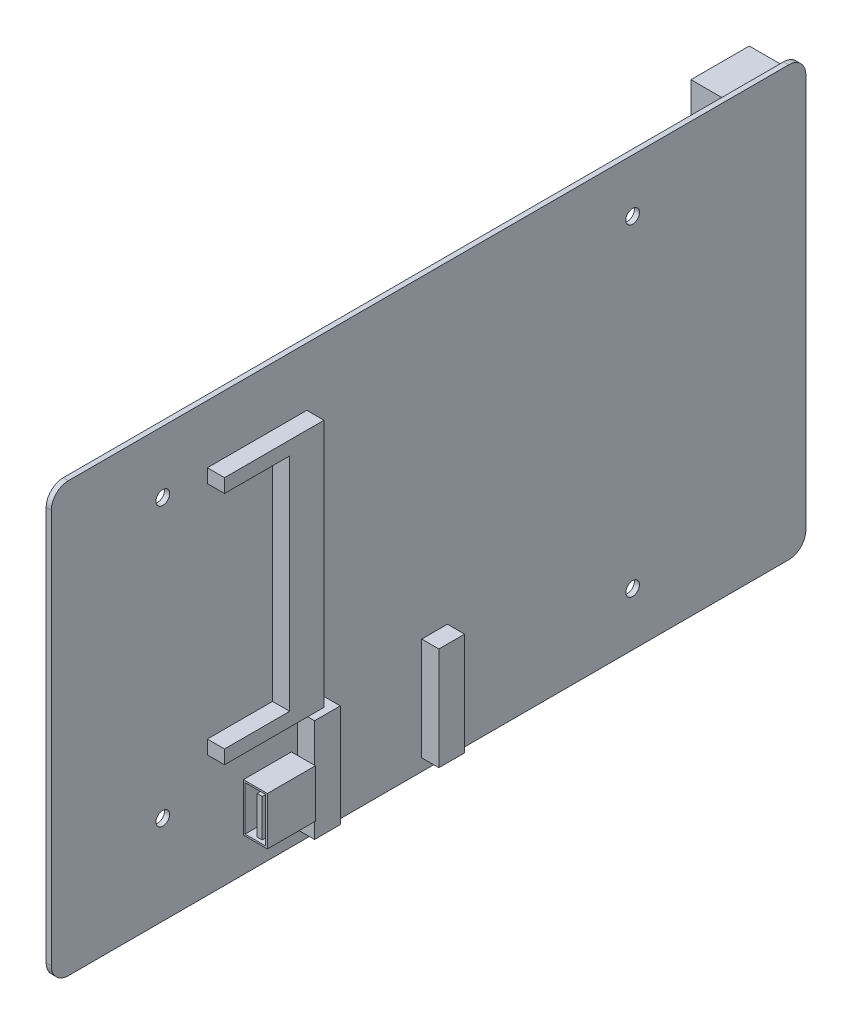
SolidWorks part; units mm, degrees
ref_plane "前视基准面" through (0, 0, 0) normal (0, 0, 1) x (1, 0, 0)
ref_plane "上视基准面" through (0, 0, 0) normal (0, 1, 0) x (1, 0, 0)
ref_plane "右视基准面" through (0, 0, 0) normal (1, 0, 0) x (0, 0, -1)
sketch "草图1" plane through (0, 0, 0) normal (1, 0, 0) x (0, 0, -1)
  line L1 (110, 62.5) -> (-110, 62.5)
  line L2 (110, 62.5) -> (110, -62.5)
  line L3 (110, -62.5) -> (-110, -62.5)
  line L4 (-110, 62.5) -> (-110, -62.5)
  line L5 (110, 62.5) -> (-110, -62.5) construction
  line L6 (110, -62.5) -> (-110, 62.5) construction
  point P0 (0, 0)
  dimension "D1" = 220
  dimension "D2" = 125
extrude "凸台-拉伸1" add sketch "草图1" against normal blind 1.5
fillet "圆角1" radius 5 4 edges at (-0.75, -62.5, -110) (-0.75, -62.5, 110) (-0.75, 62.5, -110) (-0.75, 62.5, 110)
sketch "草图2" plane through (0, 0, 0) normal (1, 0, 0) x (0, 0, -1)
  line L0 (-105, -62.5) -> (105, -62.5) construction
  line L1 (-39, -27.5) -> (-5, -27.5) construction
  line L2 (-39, -27.5) -> (-39, -60.5) construction
  line L3 (-39, -60.5) -> (-5, -60.5) construction
  line L4 (60, -27.5) -> (60, -60.5) construction
  line L5 (-39, -27.5) -> (60, -60.5) construction
  line L6 (-39, -60.5) -> (60, -27.5) construction
  line L7 (-73, 48.5) -> (-35.5, 48.5) construction
  line L8 (-73, 48.5) -> (-73, -30) construction
  line L9 (-73, -30) -> (-35.5, -30) construction
  line L10 (-35.5, 48.5) -> (-35.5, -30) construction
  line L11 (-73, 48.5) -> (-35.5, -30) construction
  line L12 (-73, -30) -> (-35.5, 48.5) construction
  line L13 (-110, 57.5) -> (-110, -57.5) construction
  line L14 (105, 62.5) -> (-105, 62.5) construction
  line L15 (-35.5, 45.5) -> (-64.5, 45.5)
  line L16 (-64.5, 45.5) -> (-64.5, 41.5)
  line L17 (-64.5, 41.5) -> (-45.5, 41.5)
  line L18 (-45.5, 41.5) -> (-45.5, -23)
  line L19 (-45.5, -23) -> (-64.5, -23)
  line L20 (-64.5, -23) -> (-64.5, -27)
  line L21 (-64.5, -27) -> (-35.5, -27)
  line L22 (-35.5, -27) -> (-35.5, 45.5)
  line L23 (-5, -27.5) -> (-5, -60.5) construction
  line L24 (-3.5, -27.5) -> (-3.5, -60.5) construction
  line L25 (-3.5, -27.5) -> (60, -27.5) construction
  line L26 (-3.5, -60.5) -> (60, -60.5) construction
  line L28 (-38.25, -29) -> (-30.75, -29)
  line L29 (-38.25, -29) -> (-38.25, -59)
  line L30 (-38.25, -59) -> (-30.75, -59)
  line L31 (-30.75, -29) -> (-30.75, -59)
  line L32 (-2, -29) -> (5.5, -29)
  line L33 (-2, -29) -> (-2, -59)
  line L34 (-2, -59) -> (5.5, -59)
  line L35 (5.5, -29) -> (5.5, -59)
  point P0 (10.5, -44)
  point P5 (-54.25, 9.25)
  dimension "D1" = 33
  dimension "D2" = 99
  dimension "D3" = 2
  dimension "D4" = 71
  dimension "D5" = 37.5
  dimension "D6" = 37
  dimension "D7" = 14
  dimension "D8" = 78.5
  dimension "D9" = 3
  dimension "D10" = 4
  dimension "D11" = 4
  dimension "D12" = 3
  dimension "D13" = 29
  dimension "D14" = 10
  dimension "D15" = 34
  dimension "D16" = 1.5
  dimension "D17" = 1.5
  dimension "D18" = 30
  dimension "D19" = 1.5
  dimension "D20" = 7.5
  dimension "D21" = 1.5
extrude "凸台-拉伸2" add sketch "草图2" along normal blind 5
sketch "草图3" plane through (0, 0, 0) normal (1, 0, 0) x (0, 0, -1)
  line L0 (-39, -27.5) -> (-39, -60.5) construction
  line L1 (-54, -38.5) -> (-40, -38.5)
  line L2 (-54, -38.5) -> (-54, -52.5)
  line L3 (-54, -52.5) -> (-40, -52.5)
  line L4 (-40, -38.5) -> (-40, -52.5)
  line L5 (-105, -62.5) -> (105, -62.5) construction
  dimension "D1" = 1
  dimension "D2" = 14
  dimension "D3" = 14
  dimension "D4" = 10
extrude "凸台-拉伸3" add sketch "草图3" along normal blind 7
sketch "草图4" plane through (0, 0, 54) normal (0, 0, 1) x (1, 0, 0)
  line L0 (7, -38.5) -> (0, -38.5) construction
  line L1 (0.5, -39) -> (6.5, -39)
  line L2 (0.5, -39) -> (0.5, -52)
  line L3 (0.5, -52) -> (6.5, -52)
  line L4 (6.5, -39) -> (6.5, -52)
  line L5 (4, -40) -> (5.5, -40)
  line L6 (4, -40) -> (4, -51)
  line L7 (4, -51) -> (5.5, -51)
  line L8 (5.5, -40) -> (5.5, -51)
  line L9 (7, -38.5) -> (7, -52.5) construction
  line L10 (7, -52.5) -> (0, -52.5) construction
  line L11 (0, -27.5) -> (0, -60.5) construction
  dimension "D1" = 0.5
  dimension "D2" = 0.5
  dimension "D3" = 0.5
  dimension "D4" = 0.5
  dimension "D5" = 1
  dimension "D6" = 1
  dimension "D7" = 1
  dimension "D8" = 1.5
extrude "切除-拉伸1" cut sketch "草图4" against normal blind 10
sketch "草图5" plane through (0, 0, 0) normal (1, 0, 0) x (0, 0, -1)
  line L0 (-110, 57.5) -> (-110, -57.5) construction
  line L1 (105, 62.5) -> (-105, 62.5) construction
  line L2 (-77.5, 44.5) -> (-77.5, 19.9461) construction
  line L3 (59.5, 47) -> (59.5, 24.1556) construction
  circle A0 centre (-77.5, 44.5) radius 2
  circle A1 centre (-77.5, -36.5) radius 2
  circle A2 centre (59.5, 47) radius 2
  circle A3 centre (59.5, -47) radius 2
  dimension "D1" = 4
  dimension "D6" = 137
  dimension "D2" = 32.5
  dimension "D3" = 18
  dimension "D4" = 81
  dimension "D5" = 15.5
  dimension "D7" = 94
extrude "切除-拉伸2" cut sketch "草图5" against normal through all
sketch "草图6" plane through (-1.5, 0, 0) normal (-1, 0, 0) x (0, 0, 1)
  line L0 (-105, 62.5) -> (105, 62.5) construction
  line L1 (-47.5, 42.5) -> (35, 42.5)
  line L2 (-47.5, 42.5) -> (-47.5, -21)
  line L3 (-47.5, -21) -> (35, -21)
  line L4 (35, 42.5) -> (35, -21)
  line L5 (110, 57.5) -> (110, -57.5) construction
  dimension "D1" = 20
  dimension "D2" = 63.5
  dimension "D3" = 82.5
  dimension "D4" = 75
extrude "凸台-拉伸4" add sketch "草图6" along normal blind 18
fillet "圆角2" radius 1 2 edges at (-19.5, 10.75, -47.5) (-19.5, 10.75, 35)
sketch "草图7" plane through (-19.5, 0, 0) normal (-1, 0, 0) x (0, 0, 1)
  line L0 (-47.5, 42.5) -> (-47.5, -21) construction
  line L1 (-47.5, -17.5) -> (35, -17.5)
  line L2 (-47.5, -17.5) -> (-47.5, -20)
  line L3 (-47.5, -20) -> (35, -20)
  line L4 (35, -17.5) -> (35, -20)
  line L5 (35, -21) -> (35, 42.5) construction
  line L6 (-47.5, -21) -> (35, -21) construction
  dimension "D1" = 1
  dimension "D2" = 2.5
extrude "切除-拉伸3" cut sketch "草图7" against normal blind 10
pattern_linear "阵列(线性)1" count 18 spacing 3.4 along (0, 1, 0) of "切除-拉伸3"
sketch "草图8" plane through (-19.5, 0, 0) normal (-1, 0, 0) x (0, 0, 1)
  line L0 (35, 42.5) -> (-47.5, 42.5) construction
  line L1 (-31.5, 42.5) -> (-30, 42.5)
  line L2 (-31.5, 42.5) -> (-31.5, -21)
  line L3 (-31.5, -21) -> (-30, -21)
  line L4 (-30, 42.5) -> (-30, -21)
  line L5 (-46.5, -21) -> (34, -21) construction
  line L6 (-47.5, -17.5) -> (-47.5, -20) construction
  dimension "D1" = 1.5
  dimension "D2" = 16
extrude "切除-拉伸4" cut sketch "草图8" against normal blind 10
pattern_linear "阵列(线性)2" count 5 spacing 11 along (0, 0, 1) of "切除-拉伸4"
sketch "草图9" plane through (-1.5, 0, 0) normal (-1, 0, 0) x (0, 0, 1)
  line L0 (105, -62.5) -> (-105, -62.5) construction
  line L1 (-75.5, 0.5) -> (-66.5, 0.5) construction
  line L2 (-75.5, 0.5) -> (-75.5, -40.5) construction
  line L3 (-75.5, -40.5) -> (-66.5, -40.5) construction
  line L4 (-66.5, 0.5) -> (-66.5, -40.5) construction
  line L5 (-110, -57.5) -> (-110, 57.5) construction
  line L7 (-75.5, -40.5) -> (-66.75, -40.5)
  line L8 (-75.5, -40.5) -> (-75.5, -1.5)
  line L9 (-75.5, -1.5) -> (-66.75, -1.5)
  line L10 (-66.75, -40.5) -> (-66.75, -1.5)
  dimension "D1" = 22
  dimension "D2" = 41
  dimension "D3" = 9
  dimension "D4" = 34.5
  dimension "D5" = 0.5
  dimension "D6" = 2
extrude "凸台-拉伸5" add sketch "草图9" along normal blind 11
sketch "草图10" plane through (-12.5, 0, 0) normal (-1, 0, 0) x (0, 0, 1)
  line L0 (-66.75, -1.5) -> (-75.5, -1.5) construction
  line L1 (-72.5, -27) -> (-70.5, -27)
  line L2 (-72.5, -27) -> (-72.5, -38.5)
  line L3 (-72.5, -38.5) -> (-70.5, -38.5)
  line L4 (-70.5, -27) -> (-70.5, -38.5)
  line L5 (-72.5, -3.5) -> (-70.5, -3.5)
  line L6 (-72.5, -3.5) -> (-72.5, -25.5)
  line L7 (-72.5, -25.5) -> (-70.5, -25.5)
  line L8 (-70.5, -3.5) -> (-70.5, -25.5)
  line L9 (-75.5, -1.5) -> (-75.5, -40.5) construction
  dimension "D1" = 11.5
  dimension "D2" = 22
  dimension "D3" = 2
  dimension "D4" = 1.5
  dimension "D5" = 3
  dimension "D6" = 2
extrude "切除-拉伸5" cut sketch "草图10" against normal blind 7.5
sketch "草图11" plane through (-1.5, 0, 0) normal (-1, 0, 0) x (0, 0, 1)
  line L0 (-110, -57.5) -> (-110, 57.5) construction
  line L1 (-110, 56.5) -> (-93, 56.5)
  line L2 (-110, 56.5) -> (-110, 42.5)
  line L3 (-110, 42.5) -> (-93, 42.5)
  line L4 (-93, 56.5) -> (-93, 42.5)
  line L5 (-105, 62.5) -> (105, 62.5) construction
  dimension "D1" = 6
  dimension "D2" = 14
  dimension "D3" = 17
extrude "凸台-拉伸6" add sketch "草图11" along normal blind 15
sketch "草图12" plane through (0, 0, -110) normal (0, 0, -1) x (-1, 0, 0)
  line L0 (16.5, 56.5) -> (16.5, 42.5) construction
  line L1 (10.5, 56) -> (16, 56)
  line L2 (10.5, 56) -> (10.5, 43)
  line L3 (10.5, 43) -> (16, 43)
  line L4 (16, 56) -> (16, 43)
  line L5 (2, 56) -> (7.5, 56)
  line L6 (2, 56) -> (2, 43)
  line L7 (2, 43) -> (7.5, 43)
  line L8 (7.5, 56) -> (7.5, 43)
  line L9 (13.5, 55) -> (15, 55)
  line L10 (13.5, 55) -> (13.5, 44)
  line L11 (13.5, 44) -> (15, 44)
  line L12 (15, 55) -> (15, 44)
  line L13 (5, 55) -> (6.5, 55)
  line L14 (5, 55) -> (5, 44)
  line L15 (5, 44) -> (6.5, 44)
  line L16 (6.5, 55) -> (6.5, 44)
  line L17 (16.5, 56.5) -> (1.5, 56.5) construction
  line L18 (16.5, 42.5) -> (1.5, 42.5) construction
  dimension "D1" = 0.5
  dimension "D2" = 0.5
  dimension "D3" = 1
  dimension "D4" = 1
  dimension "D5" = 1
  dimension "D6" = 1
  dimension "D7" = 1.5
  dimension "D8" = 3
  dimension "D9" = 0.5
  dimension "D10" = 14
extrude "切除-拉伸6" cut sketch "草图12" against normal blind 10
sketch "草图13" plane through (-1.5, 0, 0) normal (-1, 0, 0) x (0, 0, 1)
  line L0 (-110, -57.5) -> (-110, 42.5) construction
  line L1 (-110, 32) -> (-94, 32)
  line L2 (-110, 32) -> (-110, 15.5)
  line L3 (-110, 15.5) -> (-94, 15.5)
  line L4 (-94, 32) -> (-94, 15.5)
  line L5 (-110, 42.5) -> (-93, 42.5) construction
  dimension "D1" = 16
  dimension "D2" = 16.5
  dimension "D3" = 10.5
extrude "凸台-拉伸7" add sketch "草图13" along normal blind 13.5
sketch "草图14" plane through (0, 0, -110) normal (0, 0, -1) x (-1, 0, 0)
  line L0 (11, 20.75) -> (11, 17.5)
  line L1 (3.5, 30) -> (11, 30)
  line L2 (3.5, 30) -> (3.5, 17.5)
  line L3 (3.5, 17.5) -> (11, 17.5)
  line L4 (11, 30) -> (11, 26.75)
  line L5 (11, 26.75) -> (14, 26.75)
  line L7 (11, 20.75) -> (14, 20.75)
  line L8 (14, 26.75) -> (14, 20.75)
  line L9 (15, 32) -> (15, 15.5) construction
  line L10 (15, 15.5) -> (1.5, 15.5) construction
  line L11 (15, 32) -> (1.5, 32) construction
  line L12 (1.5, 42.5) -> (1.5, -21) construction
  line L13 (3.5, 23.75) -> (24.5, 23.75) construction
  point P18 (14, 23.75)
  dimension "D1" = 4
  dimension "D2" = 2
  dimension "D3" = 2
  dimension "D4" = 2
  dimension "D5" = 1
  dimension "D6" = 6
extrude "切除-拉伸7" cut sketch "草图14" against normal blind 13.5
pattern_linear "阵列(线性)3" count 2 spacing 20.5 along (0, -1, 0) of "凸台-拉伸7", "切除-拉伸7"
